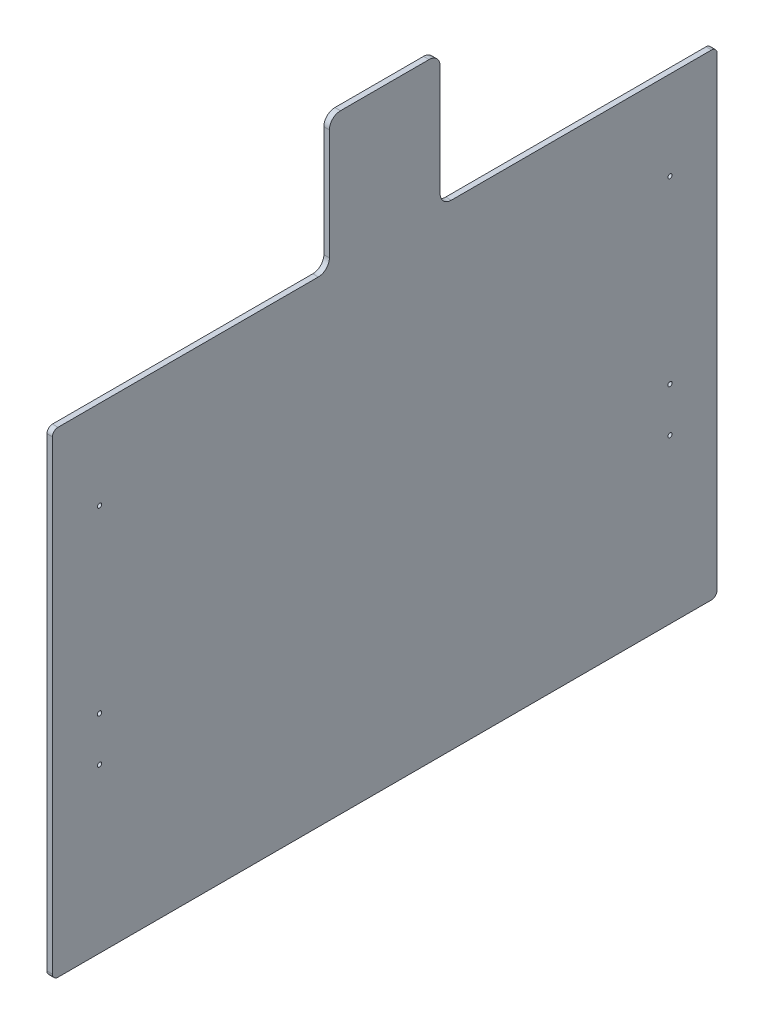
SolidWorks part; units mm, degrees
material "PE High Density"
ref_plane "Front Plane" through (0, 0, 0) normal (0, 0, 1) x (1, 0, 0)
ref_plane "Top Plane" through (0, 0, 0) normal (0, 1, 0) x (1, 0, 0)
ref_plane "Right Plane" through (0, 0, 0) normal (1, 0, 0) x (0, 0, -1)
sketch "Sketch1" plane through (0, 0, 0) normal (1, 0, 0) x (0, 0, -1)
  line L0 (457.2, 546.1) -> (755.65, 546.1)
  line L1 (6.35, 0) -> (755.65, 0)
  line L2 (0, 6.35) -> (0, 539.75)
  line L3 (6.35, 546.1) -> (304.8, 546.1)
  line L4 (762, 6.35) -> (762, 539.75)
  line L6 (317.5, 558.8) -> (317.5, 685.8)
  line L7 (330.2, 698.5) -> (431.8, 698.5)
  line L8 (444.5, 558.8) -> (444.5, 685.8)
  arc A0 (6.35, 0) -> (0, 6.35) centre (6.35, 6.35) cw
  arc A1 (755.65, 0) -> (762, 6.35) centre (755.65, 6.35) ccw
  arc A2 (755.65, 546.1) -> (762, 539.75) centre (755.65, 539.75) cw
  arc A3 (0, 539.75) -> (6.35, 546.1) centre (6.35, 539.75) cw
  circle A4 centre (53.975, 444.5) radius 2.4575
  circle A5 centre (708.025, 444.5) radius 2.4575
  circle A6 centre (708.025, 238.125) radius 2.4575
  circle A8 centre (53.975, 238.125) radius 2.4574
  circle A9 centre (53.975, 187.325) radius 2.4574
  circle A10 centre (708.025, 187.325) radius 2.4575
  arc A11 (304.8, 546.1) -> (317.5, 558.8) centre (304.8, 558.8) ccw
  arc A12 (457.2, 546.1) -> (444.5, 558.8) centre (457.2, 558.8) cw
  arc A13 (431.8, 698.5) -> (444.5, 685.8) centre (431.8, 685.8) cw
  arc A14 (317.5, 685.8) -> (330.2, 698.5) centre (330.2, 685.8) cw
  point P7 (0, 0)
  point P12 (762, 546.1)
  point P15 (0, 546.1)
  point P34 (317.5, 546.1)
  point P39 (444.5, 698.5)
  point P42 (317.5, 698.5)
  dimension "D3" = 6.35
  dimension "D6" = 4.9149
  dimension "D11" = 53.975
  dimension "D13" = 50.8
  dimension "D17" = 12.7
  dimension "D1" = 546.1
  dimension "D2" = 762
  dimension "D4" = 654.05
  dimension "D5" = 101.6
  dimension "D9" = 53.975
  dimension "D10" = 206.375
  dimension "D12" = 50.8
  dimension "D14" = 127
  dimension "D15" = 317.5
  dimension "D16" = 152.4
  dimension "D7" = 2
  dimension "D8" = 2
extrude "Boss-Extrude1" add sketch "Sketch1" along normal blind 6.35
sketch "Sketch3" plane through (6.35, 0, 0) normal (1, 0, 0) x (0, 0, -1)
  line L13 (304.8, 546.1) -> (6.35, 546.1) construction
  line L14 (0, 539.75) -> (0, 6.35) construction
  circle A2 centre (133.35, 415.925) radius 2.4575
  circle A3 centre (381, 415.925) radius 2.4574
  circle A4 centre (628.65, 415.925) radius 2.4575
  dimension "D2" = 130.175
  dimension "D12" = 4.9149
  dimension "D6" = 133.35
  dimension "D4" = 247.65
  dimension "D5" = 247.65
extrude "Cut-Extrude2" [suppressed] cut sketch "Sketch3" against normal through all
